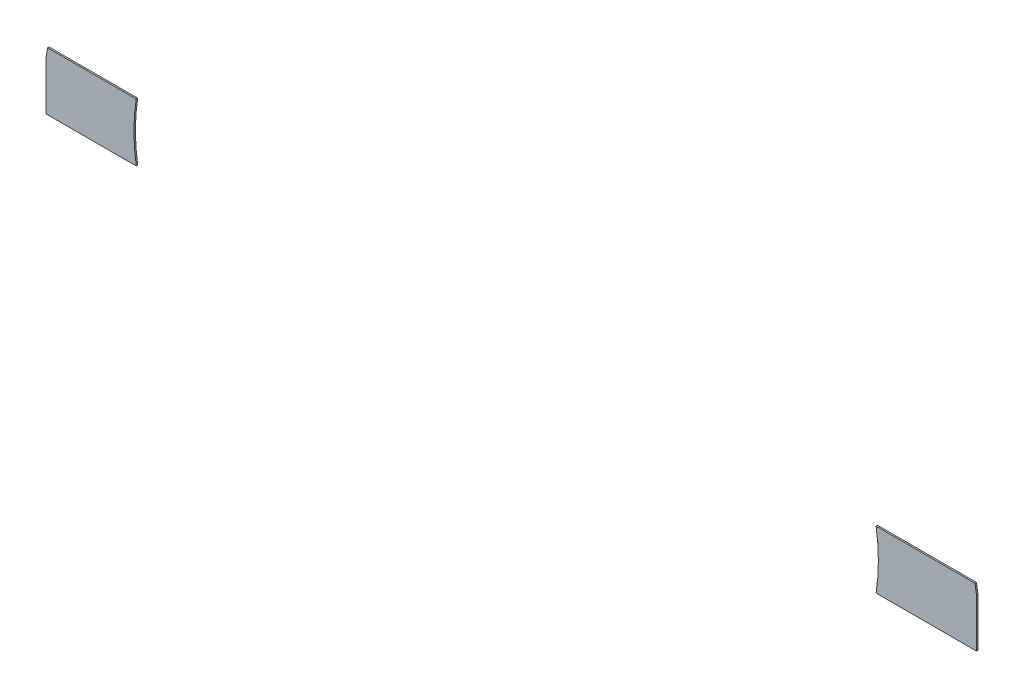
SolidWorks part; units mm, degrees
ref_plane "Alzado" through (0, 0, 0) normal (0, 0, 1) x (1, 0, 0)
ref_plane "Planta" through (0, 0, 0) normal (0, 1, 0) x (1, 0, 0)
ref_plane "Vista lateral" through (0, 0, 0) normal (1, 0, 0) x (0, 0, -1)
sketch "Model" plane through (0, 0, 0) normal (0, 0, 1) x (1, 0, 0)
  line L0 (85.1867, 21.3577) -> (85.1867, 24.6641)
  line L1 (27.2708, 25.3577) -> (21.156, 25.3577)
  line L2 (21.0533, 21.3577) -> (27.2708, 21.3577)
  line L3 (78.2637, 21.3577) -> (85.1867, 21.3577)
  line L4 (85.084, 25.3577) -> (78.2637, 25.3577)
  line L5 (21.0533, 21.3577) -> (21.0533, 24.6641)
  arc A0 (85.1867, 24.6641) -> (85.084, 25.3577) centre (53.12, 20.2718) ccw
  arc A1 (21.156, 25.3577) -> (21.0533, 24.6641) centre (53.12, 20.2718) ccw
  arc A2 (27.2708, 25.3577) -> (27.2708, 21.3577) centre (39.9406, 23.3577) ccw
  arc A3 (78.2637, 21.3577) -> (78.2637, 25.3577) centre (65.594, 23.3577) ccw
extrude "Saliente-Extruir1" add sketch "Model" along normal blind 0.1
